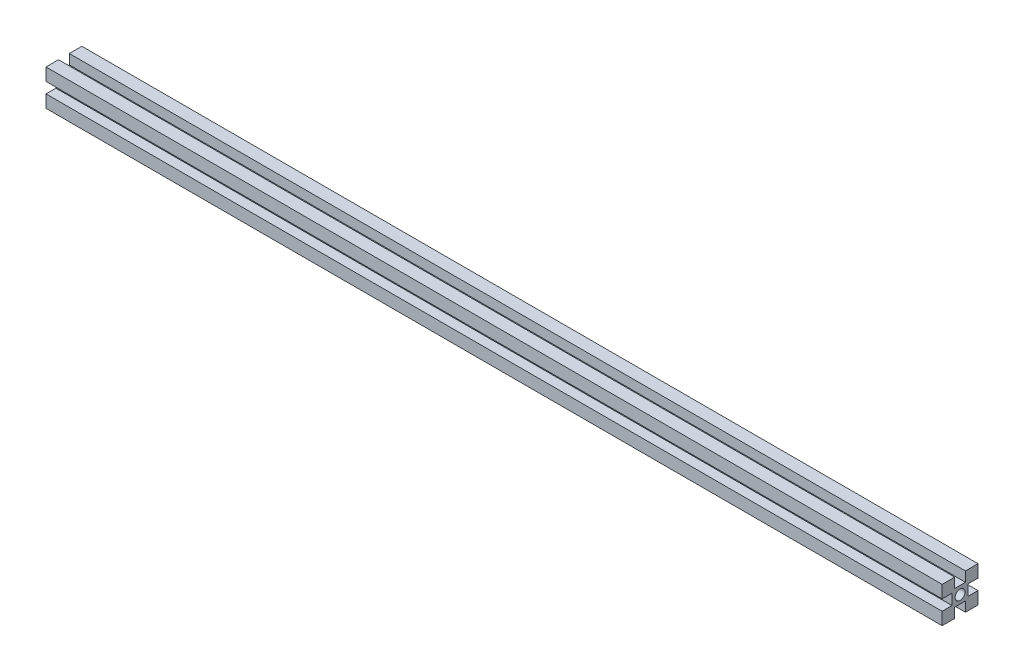
SolidWorks part; units mm, degrees
ref_plane "Plan de face" through (0, 0, 0) normal (0, 0, 1) x (1, 0, 0)
ref_plane "Plan de dessus" through (0, 0, 0) normal (0, 1, 0) x (1, 0, 0)
ref_plane "Plan de droite" through (0, 0, 0) normal (1, 0, 0) x (0, 0, -1)
ref_plane "Plan4" through (0, 0, 0) normal (-1, 0, 0) x (0, -1, 0)
sketch "Esquisse1" plane through (0, 0, 0) normal (-1, 0, 0) x (0, -1, 0)
  line L0 (-3, -10) -> (-3, -4.5)
  line L1 (-3, -4.5) -> (3, -4.5)
  line L2 (3, -4.5) -> (3, -10)
  line L3 (3, -10) -> (10, -10)
  line L4 (10, -10) -> (10, -3)
  line L5 (10, -3) -> (4.5, -3)
  line L6 (4.5, -3) -> (4.5, 3)
  line L7 (4.5, 3) -> (10, 3)
  line L8 (10, 3) -> (10, 10)
  line L9 (10, 10) -> (3, 10)
  line L10 (3, 10) -> (3, 4.5)
  line L11 (3, 4.5) -> (-3, 4.5)
  line L12 (-3, 4.5) -> (-3, 10)
  line L13 (-3, 10) -> (-10, 10)
  line L14 (-10, 10) -> (-10, 3)
  line L15 (-10, 3) -> (-4.5, 3)
  line L16 (-4.5, 3) -> (-4.5, -3)
  line L17 (-4.5, -3) -> (-10, -3)
  line L18 (-10, -3) -> (-10, -10)
  line L19 (-10, -10) -> (-3, -10)
  circle A0 centre (0, 0) radius 2.75
extrude "Boss.-Extru.1" add sketch "Esquisse1" against normal blind 500
